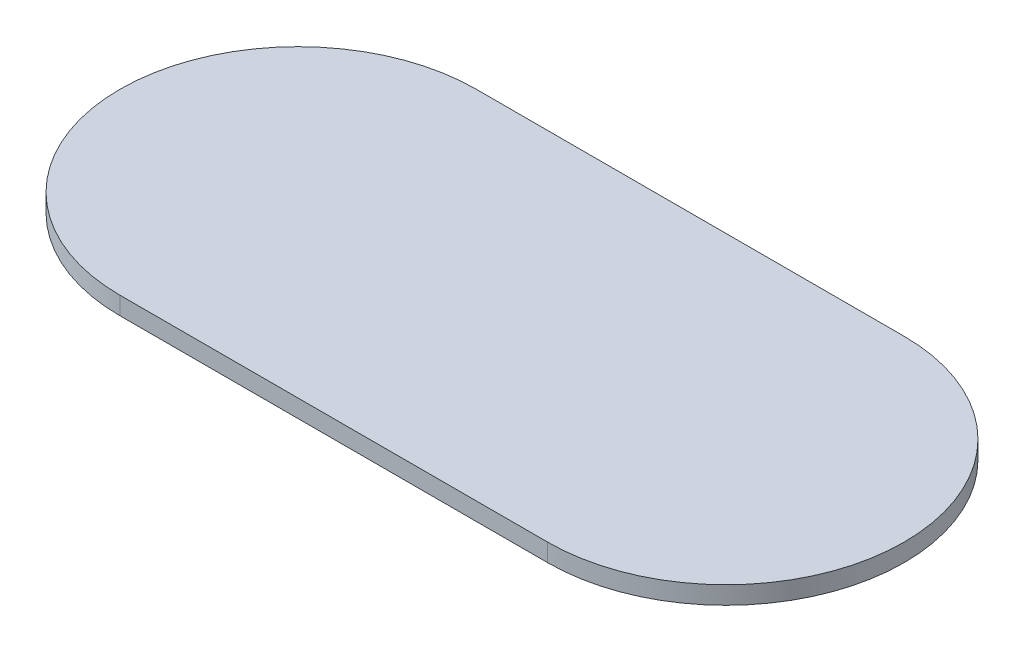
SolidWorks part; units mm, degrees
ref_plane "Front Plane" through (0, 0, 0) normal (0, 0, 1) x (1, 0, 0)
ref_plane "Top Plane" through (0, 0, 0) normal (0, 1, 0) x (1, 0, 0)
ref_plane "Right Plane" through (0, 0, 0) normal (1, 0, 0) x (0, 0, -1)
sketch "Sketch1" plane through (0, 0, 0) normal (0, 1, 0) x (1, 0, 0)
  line L0 (-76.2, 0) -> (76.2, 0)
  line L1 (-76.2, -127) -> (76.2, -127)
  arc A1 (76.2, 0) -> (76.2, -127) centre (76.2, -63.5) cw
  arc A2 (-76.2, 0) -> (-76.2, -127) centre (-76.2, -63.5) ccw
  dimension "D2" = 63.5
  dimension "D1" = 152.4
extrude "Boss-Extrude1" add sketch "Sketch1" along normal blind 6.35
